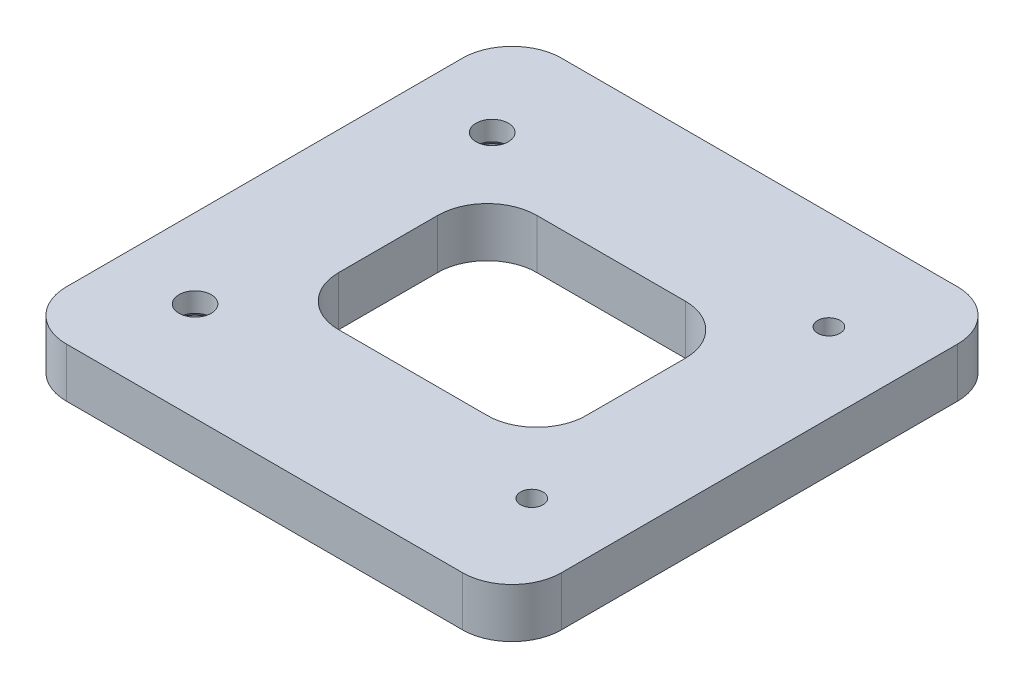
SolidWorks part; units mm, degrees
material "PLA Polyacetic Acid"
ref_plane "Front Plane" through (0, 0, 0) normal (0, 0, 1) x (1, 0, 0)
ref_plane "Top Plane" through (0, 0, 0) normal (0, 1, 0) x (1, 0, 0)
ref_plane "Right Plane" through (0, 0, 0) normal (1, 0, 0) x (0, 0, -1)
sketch "Sketch1" plane through (0, 0, 0) normal (0, 1, 0) x (1, 0, 0)
  line L1 (25, -25) -> (-25, -25)
  line L2 (25, -25) -> (25, 25)
  line L3 (25, 25) -> (-25, 25)
  line L4 (-25, -25) -> (-25, 25)
  line L5 (25, -25) -> (-25, 25) construction
  line L6 (25, 25) -> (-25, -25) construction
  point P0 (0, 0)
  dimension "D1" = 50
  dimension "D2" = 50
extrude "Boss-Extrude1" add sketch "Sketch1" along normal mid plane 5
hole_wizard "#4-40 Tapped Hole1" positions "Sketch2" profile "Sketch3" tap size "#4-40" standard "ANSI Inch" end condition up to next
sketch "Sketch2" plane through (0, 2.5, 0) normal (0, 1, 0) x (1, 0, 0)
  line L0 (0, 0) -> (26.8911, 0) construction
  line L3 (0, 4.7256) -> (0, 0) construction
  line L5 (25, -25) -> (25, 25) construction
  point P0 (17, 15)
  point P15 (17, -15)
  dimension "D1" = 8
  dimension "D2" = 30
sketch "Sketch3" plane through (17, 2.5, -15) normal (1, 0, 0) x (0, 0, 1)
  line L0 (0, 0) -> (0, 5)
  line L1 (0, 5) -> (1.1303, 5)
  line L2 (1.1303, 5) -> (1.1303, 0)
  line L5 (1.1303, 0) -> (0, 0)
  line L11 (0, -6.35) -> (0, 107.95) construction
  dimension "Thru Tap Drill Dia." = 2.2606
  dimension "Thru Tap Drill Depth" = 5
cosmetic thread "Hole Thread1" parameters "D2"=2.8448
cosmetic thread "Hole Thread2" parameters "D2"=2.8448
hole_wizard "CSK for #4 Flat Head Machine Screw (100)1" positions "Sketch4" profile "Sketch5" countersink size "#4" standard "ANSI Inch" end condition up to next
sketch "Sketch4" plane through (0, -2.5, 0) normal (0, -1, 0) x (1, 0, 0)
  line L0 (0, 0) -> (-23.5719, 0) construction
  line L3 (0, 15) -> (0, 0) construction
  line L5 (-17, 15) -> (17, 15) construction
  point P0 (-17, -15)
  point P11 (-17, 15)
  point P17 (0, 15)
sketch "Sketch5" plane through (-17, -2.5, -15) normal (1, 0, 0) x (0, 0, -1)
  line L0 (0, 0) -> (0, 5)
  line L1 (0, 5) -> (1.6319, 5)
  line L2 (1.6319, 5) -> (1.6319, 3.0284)
  line L3 (1.6319, 3.0284) -> (2.8575, 2)
  line L4 (2.8575, 2) -> (2.8575, 0)
  line L6 (2.8575, 0) -> (0, 0)
  line L7 (-1.632, 3.0284) -> (-2.8575, 2) construction
  line L11 (0, -6.35) -> (0, 107.95) construction
  dimension "Thru Hole Dia." = 3.2639
  dimension "Thru Hole Depth" = 5
  dimension "C'Sink Dia." = 5.715
  dimension "C'Sink Angle" = 100
  dimension "Head Clearance" = 2
sketch "Sketch6" plane through (0, 2.5, 0) normal (0, 1, 0) x (1, 0, 0)
  line L1 (-12.5, -10) -> (12.5, -10)
  line L2 (-12.5, -10) -> (-12.5, 10)
  line L3 (-12.5, 10) -> (12.5, 10)
  line L4 (12.5, -10) -> (12.5, 10)
  line L5 (-12.5, -10) -> (12.5, 10) construction
  line L6 (-12.5, 10) -> (12.5, -10) construction
  point P0 (0, 0)
  dimension "D1" = 20
  dimension "D2" = 25
extrude "Cut-Extrude1" cut sketch "Sketch6" against normal up to next
fillet "Fillet1" radius 5 8 edges at (-25, 0, -25) (25, 0, -25) (25, 0, 25) (-25, 0, 25) (-12.5, 0, 10) (12.5, 0, -10) (12.5, 0, 10) (-12.5, 0, -10)
